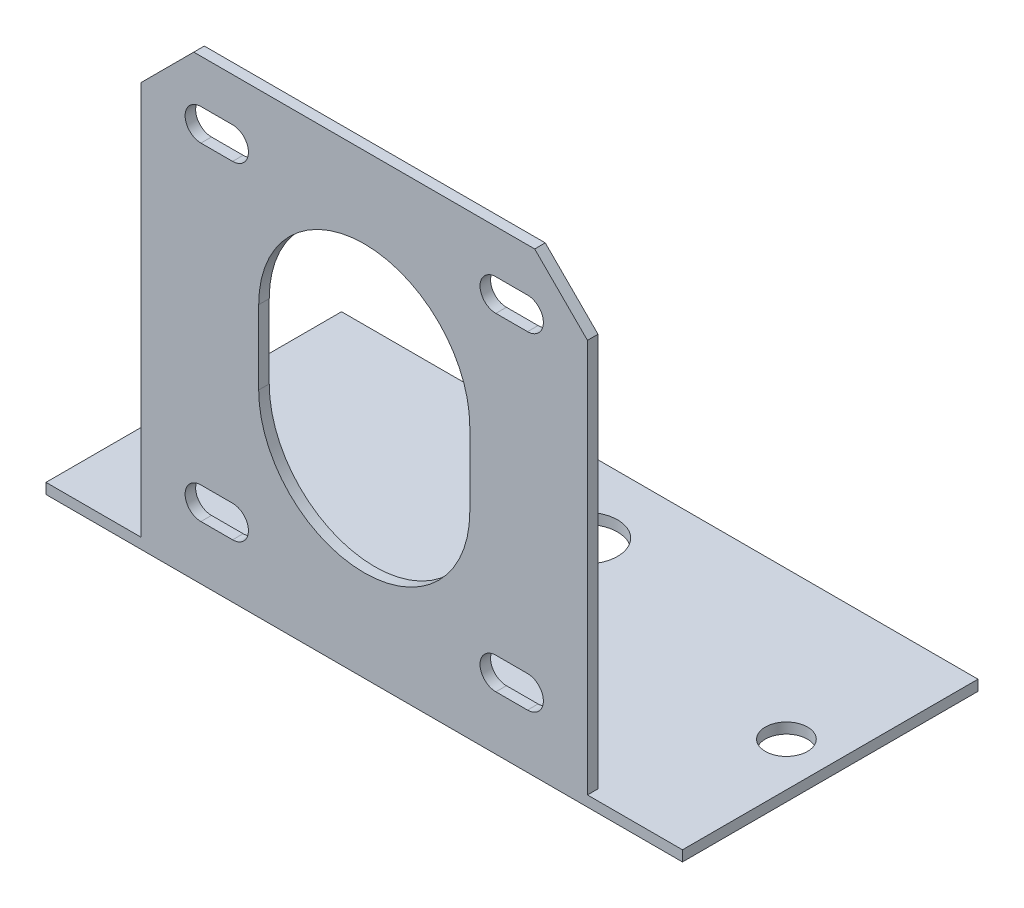
SolidWorks part; units mm, degrees
material "Alloy Steel (SS)"
ref_plane "Front Plane" through (0, 0, 0) normal (0, 0, 1) x (1, 0, 0)
ref_plane "Top Plane" through (0, 0, 0) normal (0, 1, 0) x (1, 0, 0)
ref_plane "Right Plane" through (0, 0, 0) normal (1, 0, 0) x (0, 0, -1)
sketch "Sketch1" plane through (0, 0, 0) normal (0, 0, 1) x (1, 0, 0)
  line L1 (21.15, -21.15) -> (-21.15, -21.15)
  line L2 (21.15, -21.15) -> (21.15, 21.15)
  line L3 (21.15, 21.15) -> (-21.15, 21.15)
  line L4 (-21.15, -21.15) -> (-21.15, 21.15)
  line L5 (21.15, -21.15) -> (-21.15, 21.15) construction
  line L6 (21.15, 21.15) -> (-21.15, -21.15) construction
  point P0 (0, 0)
  dimension "D1" = 42.3
  dimension "D2" = 42.3
extrude "Boss-Extrude1" add sketch "Sketch1" along normal blind 1
sketch "Sketch2" plane through (0, 0, 1) normal (0, 0, 1) x (1, 0, 0)
  line L0 (21.15, -21.15) -> (21.15, 21.15) construction
  line L1 (-21.15, -21.15) -> (21.15, -21.15)
  line L2 (-21.15, -21.15) -> (-21.15, -20.15)
  line L3 (-21.15, -20.15) -> (21.15, -20.15)
  line L4 (21.15, -21.15) -> (21.15, -20.15)
  dimension "D1" = 1
extrude "Boss-Extrude2" add sketch "Sketch2" along normal blind 10
sketch "Sketch3" plane through (0, 0, 1) normal (0, 0, 1) x (1, 0, 0)
  line L2 (-15.4709, -15.5253) -> (-12.4709, -15.5253) construction
  line L5 (-15.4709, -14.0253) -> (-12.4709, -14.0253)
  line L6 (-15.4709, -17.0253) -> (-12.4709, -17.0253)
  line L7 (-21.15, 21.15) -> (-21.15, -20.15) construction
  arc A3 (-15.4709, -14.0253) -> (-15.4709, -17.0253) centre (-15.4709, -15.5253) ccw
  arc A4 (-12.4709, -17.0253) -> (-12.4709, -14.0253) centre (-12.4709, -15.5253) ccw
  point P2 (-13.9709, -15.5253)
  dimension "D1" = 5.6791
  dimension "D2" = 3
  dimension "1.5" = 1.5
  dimension "D3" = 4.6247
extrude "Cut-Extrude2" cut sketch "Sketch3" against normal up to next (1 mm away)
mirror "Mirror1" about plane through (0, 0, 0) normal (1, 0, 0) of "Cut-Extrude2"
sketch "Sketch6" plane through (0, 0, 1) normal (0, 0, 1) x (1, 0, 0)
  line L0 (0, 3.5) -> (0, -3.5) construction
  line L1 (10, 3.5) -> (10, -3.5)
  line L2 (-10, 3.5) -> (-10, -3.5)
  arc A0 (10, 3.5) -> (-10, 3.5) centre (0, 3.5) ccw
  arc A1 (-10, -3.5) -> (10, -3.5) centre (0, -3.5) ccw
  point P2 (0, 0)
  dimension "D1" = 20
  dimension "D2" = 7
extrude "Cut-Extrude4" cut sketch "Sketch6" against normal blind 10
mirror "Mirror2" about plane through (0, 0, 0) normal (0, 1, 0) of "Mirror1", "Cut-Extrude2"
chamfer "Chamfer1" distance 5 angle 45 2 edges at (21.15, 21.15, 0.5) (-21.15, 21.15, 0.5)
sketch "Sketch8" plane through (0, 0, 0) normal (0, 0, -1) x (-1, 0, 0)
  line L0 (-21.15, -21.15) -> (21.15, -21.15)
  line L1 (21.15, -21.15) -> (21.15, -22.15)
  line L2 (21.15, -22.15) -> (-21.15, -22.15)
  line L3 (-21.15, -22.15) -> (-21.15, -21.15)
  dimension "D1" = 1
extrude "Boss-Extrude3" add sketch "Sketch8" along normal blind 27 and the other way blind 1
sketch "Sketch5" plane through (0, -20.15, 0) normal (0, 1, 0) x (1, 0, 0)
  line L0 (-21.15, -6) -> (21.15, -6) construction
  line L1 (-21.15, -11) -> (-21.15, -1) construction
  line L2 (21.15, -11) -> (21.15, -1) construction
  circle A0 centre (0, -6) radius 3
  dimension "6" = 6
extrude "Cut-Extrude3" cut sketch "Sketch5" against normal blind 22
sketch "Sketch9" plane through (21.15, 0, 0) normal (1, 0, 0) x (0, 0, -1)
  line L1 (-11, -20.15) -> (-1, -20.15)
  line L2 (-11, -20.15) -> (-11, -21.15)
  line L3 (-11, -21.15) -> (-1, -21.15)
  line L4 (-1, -20.15) -> (-1, -21.15)
  dimension "D1" = 10
  dimension "D2" = 1
extrude "Cut-Extrude5" cut sketch "Sketch9" against normal up to next
sketch "Sketch10" plane through (21.15, 0, 0) normal (1, 0, 0) x (0, 0, -1)
  line L0 (0, -21.15) -> (-1, -21.15)
  line L1 (0, -21.15) -> (27, -21.15)
  line L3 (0, -22.15) -> (27, -22.15)
  line L4 (27, -21.15) -> (27, -22.15)
  line L5 (-1, -22.15) -> (-1, 16.15) construction
  line L6 (-1, -21.15) -> (-1, -22.15)
  line L7 (-1, -22.15) -> (0, -22.15)
extrude "Boss-Extrude4" add sketch "Sketch10" along normal blind 9
mirror "Mirror3" about plane through (0, 0, 0) normal (1, 0, 0) of "Boss-Extrude4"
sketch "Sketch11" plane through (0, -21.15, 0) normal (0, 1, 0) x (1, 0, 0)
  line L0 (0, 0) -> (0, 27) construction
  line L1 (-30.15, 27) -> (30.15, 27) construction
  circle A0 centre (26, 13) radius 2
  circle A1 centre (-26, 13) radius 2
  dimension "D1" = 4
  dimension "D2" = 26
  dimension "D3" = 13
extrude "Cut-Extrude6" cut sketch "Sketch11" against normal blind 10
sketch "Sketch15" plane through (0, -21.15, 0) normal (0, 1, 0) x (1, 0, 0)
  circle A2 centre (0, 20) radius 3
  dimension "D1" = 6
  dimension "D2" = 20
extrude "Cut-Extrude8" cut sketch "Sketch15" against normal blind 10
